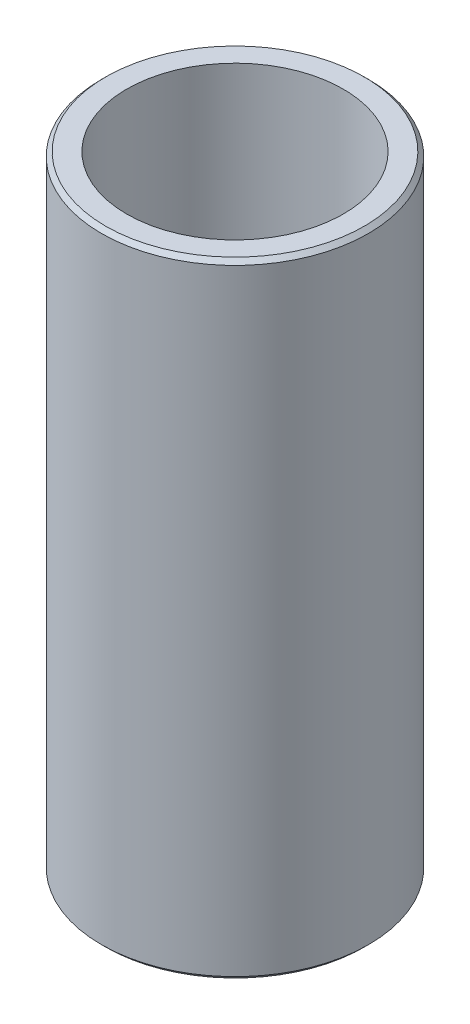
SolidWorks part; units mm, degrees
ref_plane "Front Plane" through (0, 0, 0) normal (0, 0, 1) x (1, 0, 0)
ref_plane "Top Plane" through (0, 0, 0) normal (0, 1, 0) x (1, 0, 0)
ref_plane "Right Plane" through (0, 0, 0) normal (1, 0, 0) x (0, 0, -1)
sketch "Sketch1" plane through (0, 0, 0) normal (0, 1, 0) x (1, 0, 0)
  circle A0 centre (0, 0) radius 7.94
  circle A1 centre (0, 0) radius 6.44
  dimension "D1" = 15.88
  dimension "D2" = 1.5
extrude "Boss-Extrude1" add sketch "Sketch1" along normal blind 37.13
chamfer "Chamfer1" distance 0.25 angle 45 2 edges at (0, 0, 7.94) (0, 37.13, 7.94)
